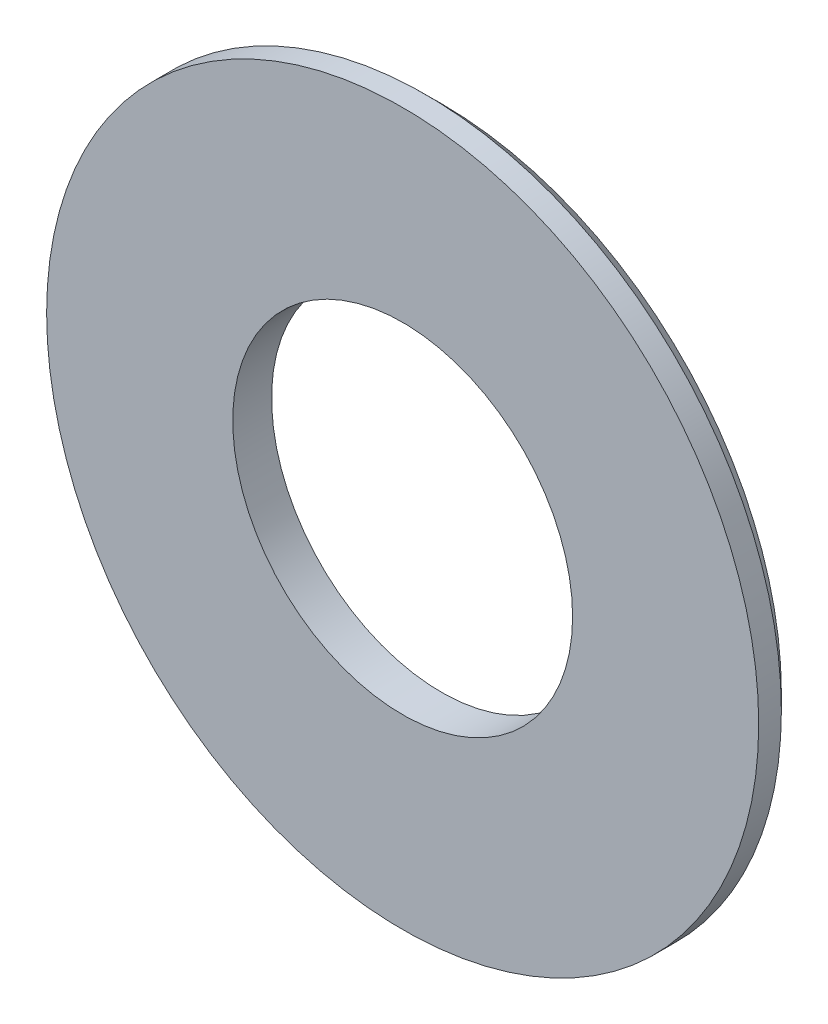
SolidWorks part; units mm, degrees
ref_plane "Alzado" through (0, 0, 0) normal (0, 0, 1) x (1, 0, 0)
ref_plane "Planta" through (0, 0, 0) normal (0, 1, 0) x (1, 0, 0)
ref_plane "Vista lateral" through (0, 0, 0) normal (1, 0, 0) x (0, 0, -1)
sketch "Croquis1" plane through (0, 0, 0) normal (0, 1, 0) x (1, 0, 0)
  line L0 (11, -1.2) -> (11, 0)
  line L1 (11, 0) -> (5.25, 0)
  line L2 (5.25, 0) -> (5.25, -1.2)
  line L3 (5.25, -1.2) -> (11, -1.2)
  line L4 (0, 0) -> (0, -1.2) construction
  dimension "D1" = 22
  dimension "D2" = 10.5
  dimension "D3" = 1.2
revolve "Revolución1" add sketch "Croquis1" angle 360 about L4
chamfer "Chaflán1" distance 0.5 angle 45 1 edges at (11, 0, 0)
